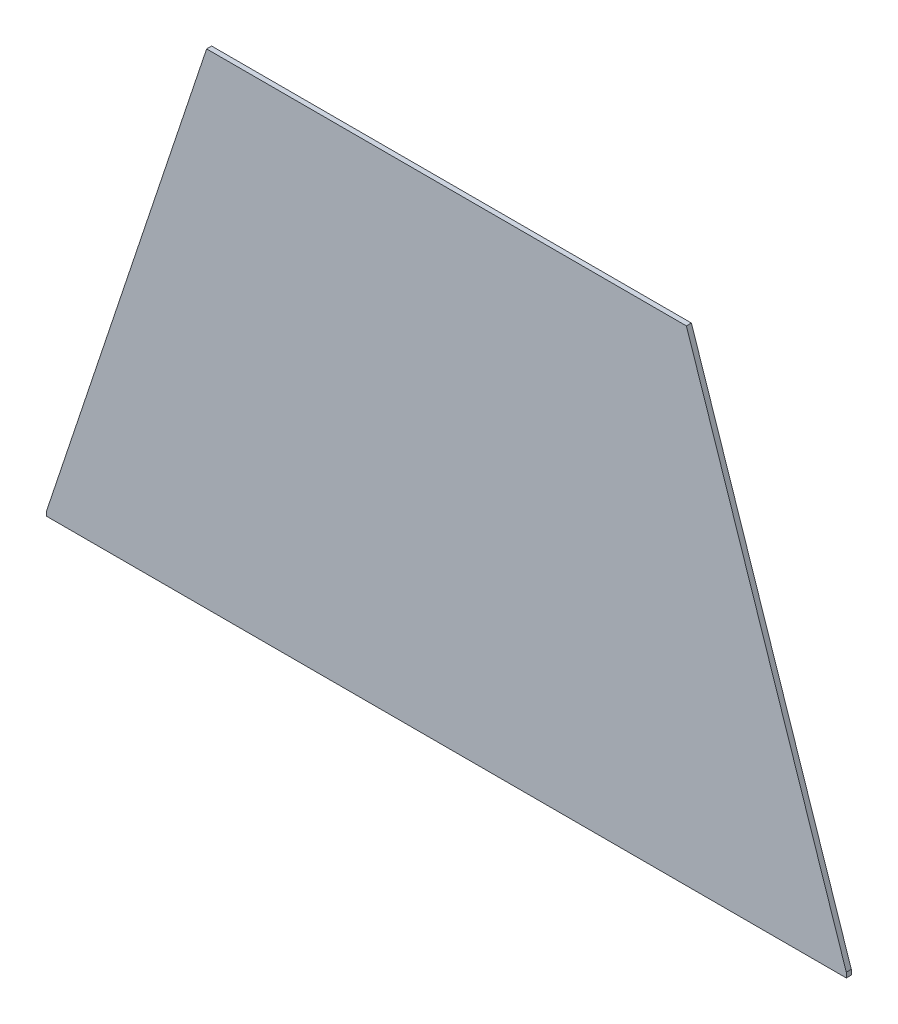
SolidWorks part; units mm, degrees
material "Carbon Fiber"
ref_plane "Front Plane" through (0, 0, 0) normal (0, 0, 1) x (1, 0, 0)
ref_plane "Top Plane" through (0, 0, 0) normal (0, 1, 0) x (1, 0, 0)
ref_plane "Right Plane" through (0, 0, 0) normal (1, 0, 0) x (0, 0, -1)
sketch "Sketch2" plane through (0, 0, 0) normal (0, 0, 1) x (1, 0, 0)
  line L0 (-127, 0) -> (-76.2, 152.4)
  line L2 (-76.2, 152.4) -> (76.2, 152.4)
  line L3 (76.2, 152.4) -> (127, 0)
  line L4 (-127, 0) -> (-127, -1.5875)
  line L5 (-127, -1.5875) -> (127, -1.5875)
  line L6 (127, -1.5875) -> (127, 0)
  dimension "D1" = 254
  dimension "D2" = 152.4
  dimension "D4" = 1.5875
extrude "Boss-Extrude1" add sketch "Sketch2" along normal blind 1.5875
